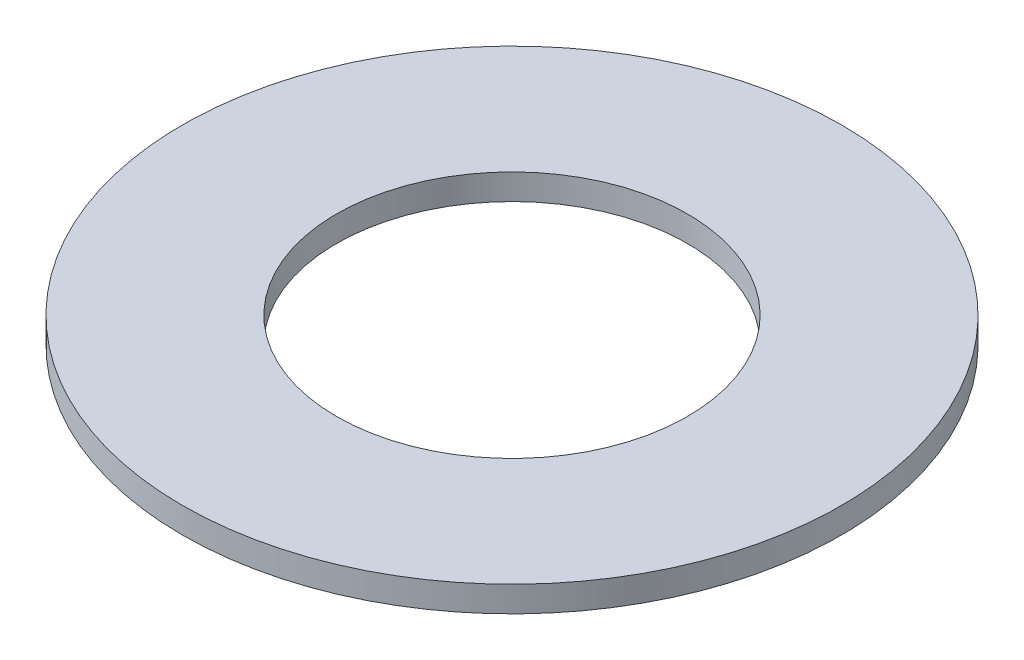
SolidWorks part; units mm, degrees
ref_plane "Front Plane" through (0, 0, 0) normal (0, 0, 1) x (1, 0, 0)
ref_plane "Top Plane" through (0, 0, 0) normal (0, 1, 0) x (1, 0, 0)
ref_plane "Right Plane" through (0, 0, 0) normal (1, 0, 0) x (0, 0, -1)
sketch "Sketch1" plane through (0, 0, 0) normal (0, 1, 0) x (1, 0, 0)
  circle A0 centre (0, 0) radius 7.7
  circle A1 centre (0, 0) radius 4.1
  dimension "D1" = 15.4
  dimension "D2" = 8.2
extrude "Boss-Extrude1" add sketch "Sketch1" along normal blind 0.6
